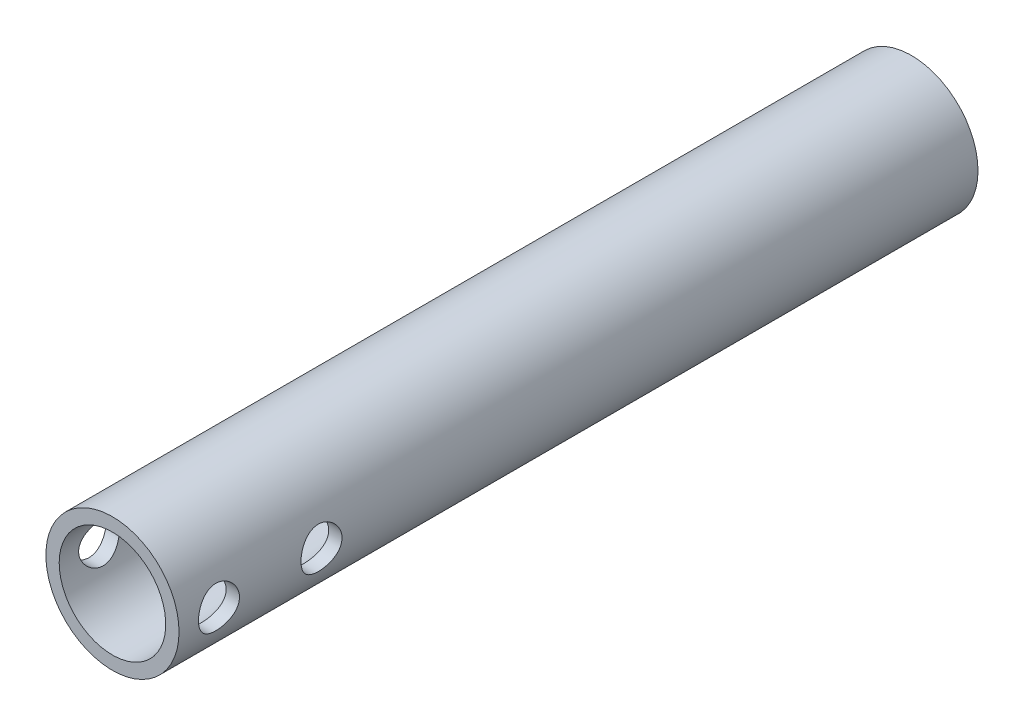
SolidWorks part; units mm, degrees
material "6061-T6 (SS)"
ref_plane "Front Plane" through (0, 0, 0) normal (0, 0, 1) x (1, 0, 0)
ref_plane "Top Plane" through (0, 0, 0) normal (0, 1, 0) x (1, 0, 0)
ref_plane "Right Plane" through (0, 0, 0) normal (1, 0, 0) x (0, 0, -1)
sketch "Sketch2" plane through (0, 0, 0) normal (0, 0, 1) x (1, 0, 0)
  circle A0 centre (0, 0) radius 6.35
  dimension "D1" = 12.7
extrude "Boss-Extrude1" add sketch "Sketch2" along normal blind 355.6
sketch "Sketch3" plane through (0, 0, 0) normal (1, 0, 0) x (0, 0, -1)
  line L0 (-355.6, 6.35) -> (-355.6, -6.35) construction
  line L1 (0, -6.35) -> (0, 6.35) construction
  circle A0 centre (-351.79, 0) radius 1.9558
  circle A1 centre (-342.011, 0) radius 1.9558
  circle A2 centre (-13.589, 0) radius 1.9558
  circle A3 centre (-3.81, 0) radius 1.9558
  dimension "D1" = 3.9116
  dimension "D2" = 3.81
  dimension "D3" = 9.779
  dimension "D4" = 3.81
  dimension "D5" = 9.779
extrude "Cut-Extrude5" cut sketch "Sketch3" against normal mid plane 355.6
sketch "Sketch4" plane through (0, 0, 0) normal (1, 0, 0) x (0, 0, -1)
  line L1 (-355.6, 6.35) -> (-355.6, -6.35) construction
  line L2 (-279.4, 24.5635) -> (0, 24.5635)
  line L3 (-279.4, 24.5635) -> (-279.4, -23.4556)
  line L4 (-279.4, -23.4556) -> (0, -23.4556)
  line L5 (0, 24.5635) -> (0, -23.4556)
  dimension "D1" = 76.2
  dimension "D2" = 0
extrude "Cut-Extrude7" cut sketch "Sketch4" against normal through all both and the other way through all
sketch "Sketch5" plane through (0, 0, 279.4) normal (0, 0, -1) x (-1, 0, 0)
  circle A0 centre (0, 0) radius 5.08
  dimension "D1" = 10.16
extrude "Cut-Extrude8" cut sketch "Sketch5" against normal through all
